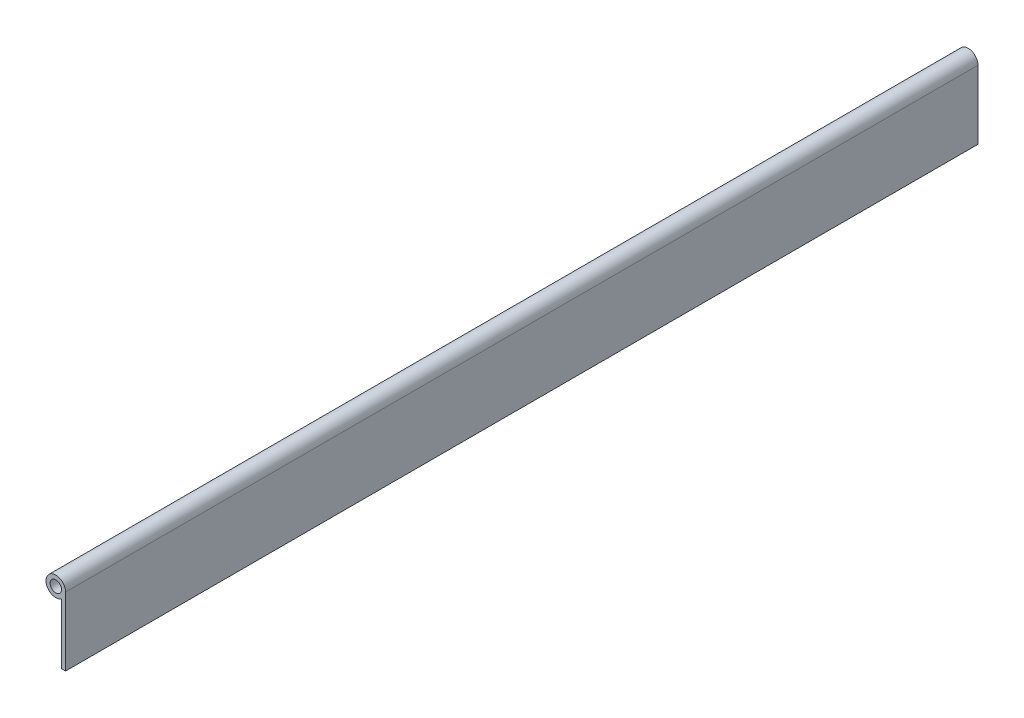
SolidWorks part; units mm, degrees
material "6061 Alloy"
ref_plane "Front Plane" through (0, 0, 0) normal (0, 0, 1) x (1, 0, 0)
ref_plane "Top Plane" through (0, 0, 0) normal (0, 1, 0) x (1, 0, 0)
ref_plane "Right Plane" through (0, 0, 0) normal (1, 0, 0) x (0, 0, -1)
sketch "Sketch1" plane through (0, 0, 0) normal (0, 0, 1) x (1, 0, 0)
  line L0 (5.461, 0) -> (5.461, -38.1)
  line L1 (5.461, -38.1) -> (3.175, -38.1)
  line L2 (3.175, -38.1) -> (3.175, -4.4432)
  circle A0 centre (0, 0) radius 3.175
  arc A1 (5.461, 0) -> (3.175, -4.4432) centre (0, 0) ccw
  circle A2 centre (0, 0) radius 5.461 construction
  dimension "D1" = 6.35
  dimension "D3" = 2.286
  dimension "D4" = 38.1
  dimension "D2" = 2.286
extrude "Boss-Extrude1" add sketch "Sketch1" along normal blind 508
sketch "Sketch2" plane through (5.461, 0, 0) normal (1, 0, 0) x (0, 0, -1)
  line L1 (-508, 5.461) -> (-482.6, 5.461)
  line L2 (-508, 5.461) -> (-508, -7.239)
  line L3 (-508, -7.239) -> (-482.6, -7.239)
  line L4 (-482.6, 5.461) -> (-482.6, -7.239)
  dimension "D1" = 12.7
  dimension "D2" = 25.4
extrude "Cut-Extrude1" [suppressed] cut sketch "Sketch2" against normal through all
pattern_linear "LPattern1" [suppressed] count 10 spacing 50.8
sketch "Sketch4" [suppressed] plane through (5.461, 0, 0) normal (1, 0, 0) x (0, 0, -1)
  line L0 (-508, -7.239) -> (-482.6, -7.239) construction
  line L1 (-508, -38.1) -> (-495.3, -38.1)
  line L2 (-508, -38.1) -> (-508, -7.239)
  line L3 (-508, -7.239) -> (-495.3, -7.239)
  line L4 (-495.3, -38.1) -> (-495.3, -7.239)
  line L5 (0, 5.461) -> (-25.4, 5.461) construction
  line L6 (0, -38.1) -> (-12.7, -38.1)
  line L7 (0, -38.1) -> (0, 5.461)
  line L8 (0, 5.461) -> (-12.7, 5.461)
  line L9 (-12.7, -38.1) -> (-12.7, 5.461)
  dimension "D1" = 12.7
extrude "Cut-Extrude2" [suppressed] cut sketch "Sketch4" against normal through all
